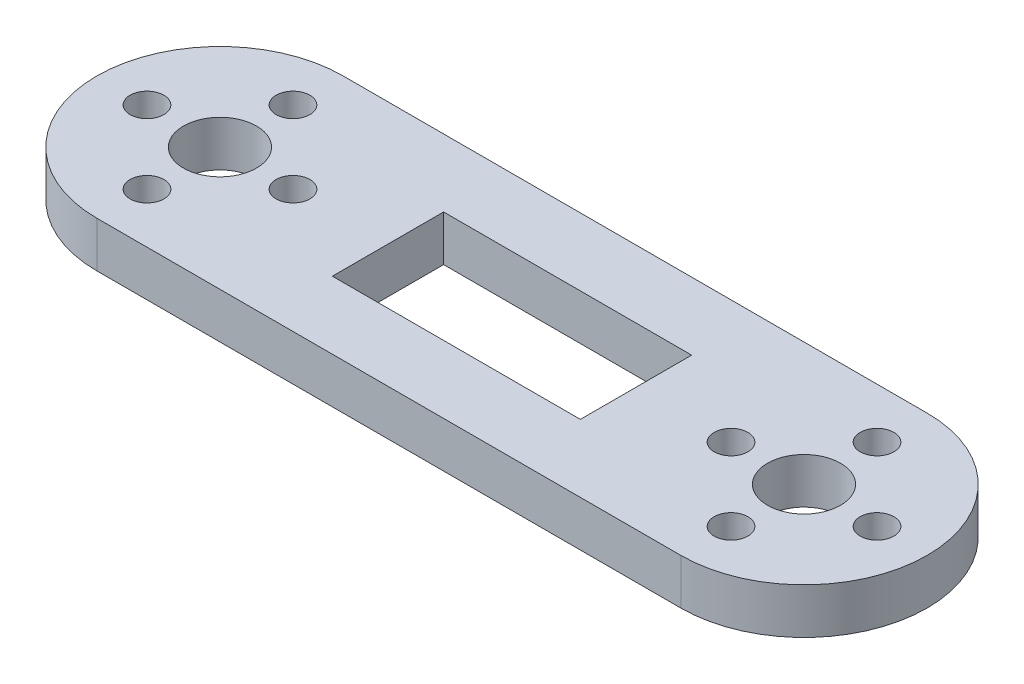
SolidWorks part; units mm, degrees
material "ABS"
ref_plane "Front Plane" through (0, 0, 0) normal (0, 0, 1) x (1, 0, 0)
ref_plane "Top Plane" through (0, 0, 0) normal (0, 1, 0) x (1, 0, 0)
ref_plane "Right Plane" through (0, 0, 0) normal (1, 0, 0) x (0, 0, -1)
ref_plane "Plane1" through (0, 5, 0) normal (0, 1, 0) x (1, 0, 0)
sketch "Sketch1" plane through (0, 5, 0) normal (0, 1, 0) x (1, 0, 0)
  line L0 (45.589, -6.096) -> (18.411, -6.096)
  line L1 (18.411, -6.096) -> (18.411, 6.096)
  line L2 (18.411, 6.096) -> (45.589, 6.096)
  line L3 (45.589, 6.096) -> (45.589, -6.096)
  line L4 (64, 13.5) -> (0, 13.5)
  line L5 (0, -13.5) -> (64, -13.5)
  circle A0 centre (56, 0) radius 1.85
  circle A1 centre (64, -8) radius 1.85
  circle A2 centre (72, 0) radius 1.85
  circle A3 centre (64, 8) radius 1.85
  circle A4 centre (64, 0) radius 4
  circle A5 centre (-8, 0) radius 1.85
  circle A6 centre (0, -8) radius 1.85
  circle A7 centre (8, 0) radius 1.85
  circle A8 centre (0, 8) radius 1.85
  circle A9 centre (0, 0) radius 4
  arc A10 (0, 13.5) -> (0, -13.5) centre (0, 0) ccw
  arc A11 (64, -13.5) -> (64, 13.5) centre (64, 0) ccw
extrude "Boss-Extrude1" add sketch "Sketch1" against normal blind 5
